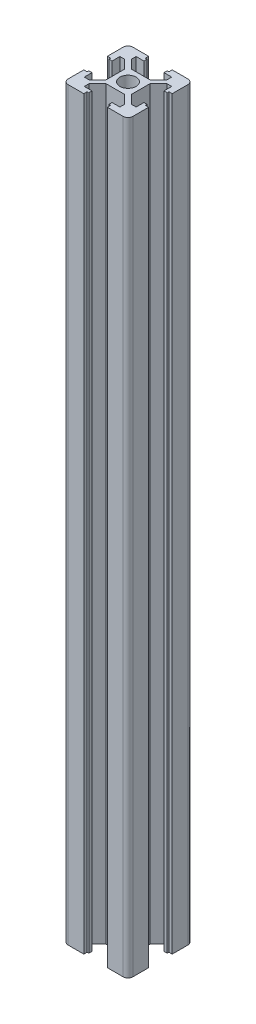
SolidWorks part; units mm, degrees
material "6063-T5"
ref_plane "前视基准面" through (0, 0, 0) normal (0, 0, 1) x (1, 0, 0)
ref_plane "上视基准面" through (0, 0, 0) normal (0, 1, 0) x (1, 0, 0)
ref_plane "右视基准面" through (0, 0, 0) normal (1, 0, 0) x (0, 0, -1)
sketch "草图1" plane through (0, 0, 0) normal (0, 1, 0) x (1, 0, 0)
  line L0 (0, 0) -> (13.5691, 13.5691) construction
  line L1 (0, 0) -> (18.8639, 0) construction
  line L2 (0, 0) -> (0, 13.1158) construction
  line L8 (3.9, 2.8393) -> (3.9, -2.8393)
  line L9 (10, 10) -> (10, 3.65)
  line L10 (10, 3.65) -> (9, 3.65)
  line L11 (9, 3.65) -> (9, 3.1)
  line L12 (9, 3.1) -> (8, 3.1)
  line L13 (8, 3.1) -> (8, 5.5)
  line L14 (8, 5.5) -> (6.5607, 5.5)
  line L15 (6.5607, 5.5) -> (3.9, 2.8393)
  line L16 (2.8393, 3.9) -> (-2.8393, 3.9)
  line L17 (5.5, 6.5607) -> (2.8393, 3.9)
  line L18 (5.5, 8) -> (5.5, 6.5607)
  line L19 (3.1, 8) -> (5.5, 8)
  line L20 (3.1, 9) -> (3.1, 8)
  line L21 (3.65, 9) -> (3.1, 9)
  line L22 (10, 10) -> (3.65, 10)
  line L23 (3.65, 10) -> (3.65, 9)
  line L24 (6.5607, -5.5) -> (3.9, -2.8393)
  line L25 (8, -5.5) -> (6.5607, -5.5)
  line L26 (8, -3.1) -> (8, -5.5)
  line L27 (9, -3.1) -> (8, -3.1)
  line L28 (10, -3.65) -> (9, -3.65)
  line L29 (10, -10) -> (10, -3.65)
  line L30 (10, -10) -> (3.65, -10)
  line L31 (3.65, -10) -> (3.65, -9)
  line L32 (3.65, -9) -> (3.1, -9)
  line L33 (3.1, -9) -> (3.1, -8)
  line L34 (3.1, -8) -> (5.5, -8)
  line L35 (5.5, -8) -> (5.5, -6.5607)
  line L36 (5.5, -6.5607) -> (2.8393, -3.9)
  line L37 (2.8393, -3.9) -> (-2.8393, -3.9)
  line L38 (9, -3.65) -> (9, -3.1)
  line L39 (-5.5, -6.5607) -> (-2.8393, -3.9)
  line L40 (-5.5, -8) -> (-5.5, -6.5607)
  line L41 (-3.1, -8) -> (-5.5, -8)
  line L42 (-3.1, -9) -> (-3.1, -8)
  line L43 (-3.65, -9) -> (-3.1, -9)
  line L44 (-3.65, -10) -> (-3.65, -9)
  line L45 (-9, -3.65) -> (-9, -3.1)
  line L46 (-10, -10) -> (-3.65, -10)
  line L47 (-10, -10) -> (-10, -3.65)
  line L48 (-10, -3.65) -> (-9, -3.65)
  line L49 (-9, -3.1) -> (-8, -3.1)
  line L50 (-8, -3.1) -> (-8, -5.5)
  line L51 (-8, -5.5) -> (-6.5607, -5.5)
  line L52 (-6.5607, -5.5) -> (-3.9, -2.8393)
  line L53 (-5.5, 6.5607) -> (-2.8393, 3.9)
  line L54 (-3.65, 10) -> (-3.65, 9)
  line L55 (-10, 10) -> (-3.65, 10)
  line L56 (-3.65, 9) -> (-3.1, 9)
  line L57 (-3.1, 9) -> (-3.1, 8)
  line L58 (-3.1, 8) -> (-5.5, 8)
  line L59 (-5.5, 8) -> (-5.5, 6.5607)
  line L60 (-3.9, 2.8393) -> (-3.9, -2.8393)
  line L61 (-6.5607, 5.5) -> (-3.9, 2.8393)
  line L62 (-8, 5.5) -> (-6.5607, 5.5)
  line L63 (-8, 3.1) -> (-8, 5.5)
  line L64 (-9, 3.1) -> (-8, 3.1)
  line L65 (-9, 3.65) -> (-9, 3.1)
  line L66 (-10, 3.65) -> (-9, 3.65)
  line L67 (-10, 10) -> (-10, 3.65)
  circle A0 centre (0, 0) radius 2.5
  point P11 (24.125, 24.125)
  point P25 (3.9, 0)
  point P41 (0, -3.9)
  point P57 (0, 3.9)
  point P70 (13.5691, 13.5691)
  point P71 (0, 13.1158)
  point P72 (18.8639, 0)
  dimension "D3" = 5
  dimension "D2" = 10
  dimension "D4" = 0.75
  dimension "D5" = 3.1
  dimension "D6" = 3.65
  dimension "D7" = 5.5
  dimension "D8" = 1
  dimension "D9" = 1
  dimension "D10" = 6.1
extrude "凸台-拉伸1" add sketch "草图1" along normal blind 230
fillet "圆角1" radius 1.5 4 edges at (-10, 115, 10) (10, 115, 10) (-10, 115, -10) (10, 115, -10)
